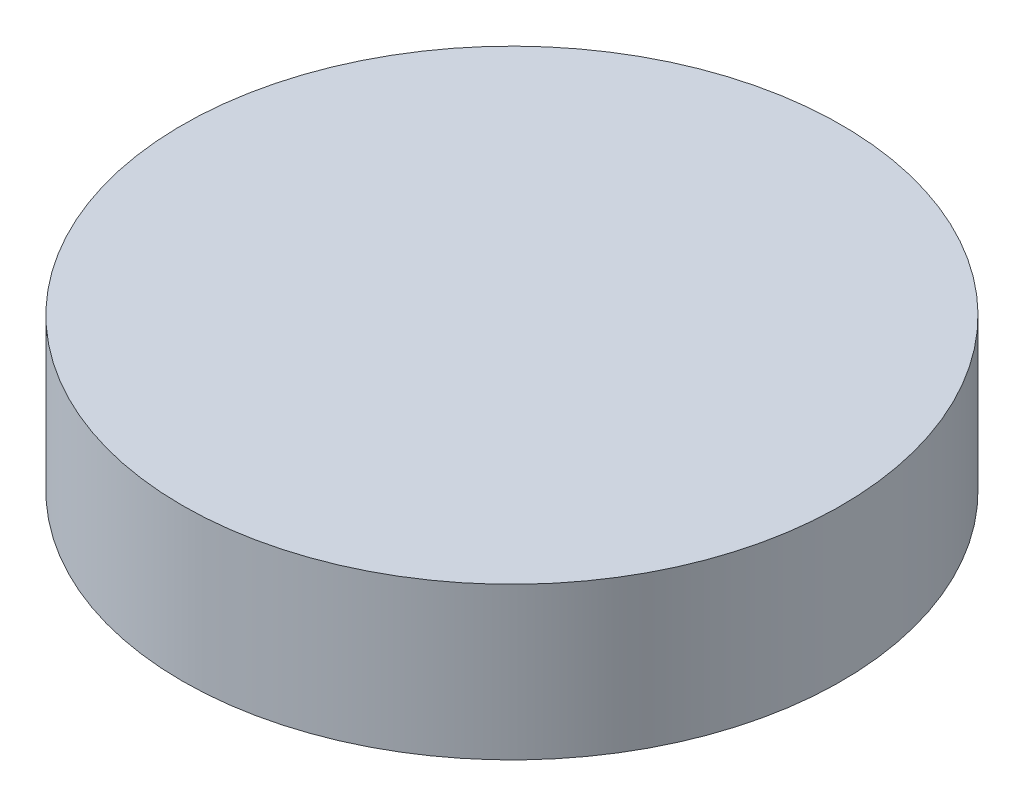
SolidWorks part; units mm, degrees
ref_plane "Front Plane" through (0, 0, 0) normal (0, 0, 1) x (1, 0, 0)
ref_plane "Top Plane" through (0, 0, 0) normal (0, 1, 0) x (1, 0, 0)
ref_plane "Right Plane" through (0, 0, 0) normal (1, 0, 0) x (0, 0, -1)
sketch "Sketch1" plane through (0, 0, 0) normal (0, 1, 0) x (1, 0, 0)
  circle A0 centre (0, 0) radius 65
  dimension "D1" = 130
extrude "Boss-Extrude1" add sketch "Sketch1" along normal blind 30
